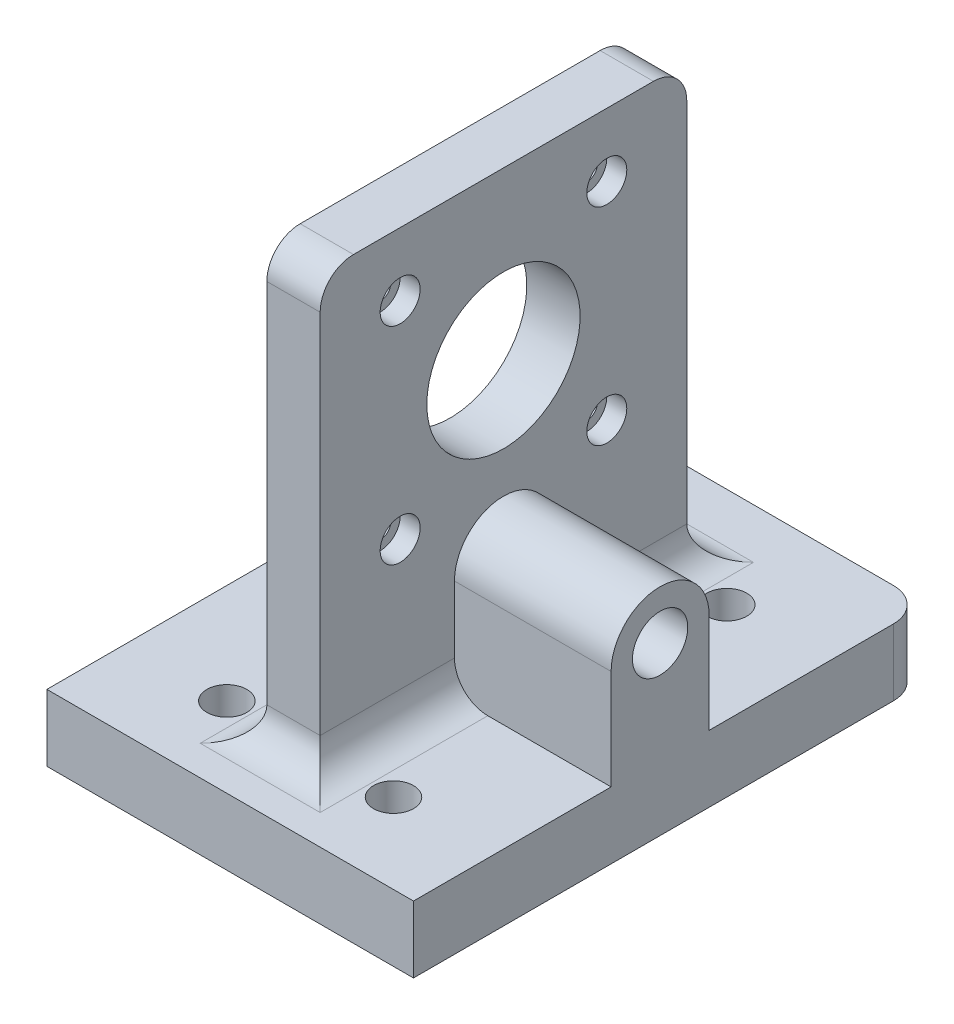
SolidWorks part; units mm, degrees
ref_plane "Front Plane" through (0, 0, 0) normal (0, 0, 1) x (1, 0, 0)
ref_plane "Top Plane" through (0, 0, 0) normal (0, 1, 0) x (1, 0, 0)
ref_plane "Right Plane" through (0, 0, 0) normal (1, 0, 0) x (0, 0, -1)
sketch "Sketch1" plane through (0, 0, 0) normal (0, 1, 0) x (1, 0, 0)
  line L1 (-27.5, 40) -> (27.5, 40)
  line L2 (-27.5, 40) -> (-27.5, -40)
  line L3 (-27.5, -40) -> (27.5, -40)
  line L4 (27.5, 40) -> (27.5, -40)
  line L5 (-27.5, 40) -> (27.5, -40) construction
  line L6 (-27.5, -40) -> (27.5, 40) construction
  point P0 (0, 0)
  dimension "D1" = 55
  dimension "D2" = 80
extrude "Boss-Extrude1" add sketch "Sketch1" along normal blind 10
sketch "Sketch6" plane through (0, 10, 0) normal (0, 1, 0) x (1, 0, 0)
  line L0 (-27.5, -40) -> (27.5, -40) construction
  circle A0 centre (-12.5, -25) radius 1.65
  dimension "D3" = 3.3
  dimension "D1" = 12.5
  dimension "D2" = 15
extrude "Cut-Extrude2" cut sketch "Sketch6" against normal blind 55
pattern_linear "LPattern1" count 3 spacing 25 along (0, 0, -1) of "Cut-Extrude2"
mirror "Mirror3" about plane through (0, 0, 0) normal (1, 0, 0) of "LPattern1", "Cut-Extrude2"
sketch "Sketch8" plane through (0, 10, 0) normal (0, 1, 0) x (1, 0, 0)
  line L1 (-4, 27.5) -> (4, 27.5)
  line L2 (-4, 27.5) -> (-4, -27.5)
  line L3 (-4, -27.5) -> (4, -27.5)
  line L4 (4, 27.5) -> (4, -27.5)
  line L5 (-4, 27.5) -> (4, -27.5) construction
  line L6 (-4, -27.5) -> (4, 27.5) construction
  point P0 (0, 0)
  dimension "D1" = 55
  dimension "D2" = 8
extrude "Boss-Extrude3" add sketch "Sketch8" along normal blind 65
fillet "Fillet3" radius 5 8 edges at (-27.5, 5, -40) (27.5, 5, -40) (0, 75, -27.5) (0, 75, 27.5) (4, 10, 0) (-4, 10, 0) (0, 10, -27.5) (0, 10, 27.5)
sketch "Sketch9" plane through (-4, 0, 0) normal (-1, 0, 0) x (0, 0, 1)
  line L0 (-22.5, 75) -> (22.5, 75) construction
  line L1 (-15.5, 65.5) -> (15.5, 65.5) construction
  line L2 (-15.5, 65.5) -> (-15.5, 34.5) construction
  line L3 (-15.5, 34.5) -> (15.5, 34.5) construction
  line L4 (15.5, 65.5) -> (15.5, 34.5) construction
  line L5 (-15.5, 65.5) -> (15.5, 34.5) construction
  line L6 (-15.5, 34.5) -> (15.5, 65.5) construction
  circle A0 centre (-15.5, 65.5) radius 1.6
  circle A1 centre (15.5, 65.5) radius 1.6
  circle A2 centre (-15.5, 34.5) radius 1.6
  circle A3 centre (15.5, 34.5) radius 1.6
  circle A4 centre (0, 50) radius 11.5
  point P0 (0, 50)
  dimension "D5" = 3.2
  dimension "D6" = 3.2
  dimension "D7" = 3.2
  dimension "D8" = 3.2
  dimension "D9" = 23
  dimension "D1" = 25
  dimension "D2" = 31
  dimension "D3" = 31
  dimension "D4" = 0
extrude "Cut-Extrude3" cut sketch "Sketch9" against normal through all
sketch "Sketch10" plane through (4, 0, 0) normal (1, 0, 0) x (0, 0, -1)
  circle A0 centre (-15.5, 65.5) radius 3
  circle A1 centre (15.5, 65.5) radius 3
  circle A2 centre (15.5, 34.5) radius 3
  circle A3 centre (-15.5, 34.5) radius 3
  dimension "D1" = 6
  dimension "D2" = 6
  dimension "D3" = 6
  dimension "D4" = 6
extrude "Cut-Extrude4" cut sketch "Sketch10" against normal blind 3
sketch "Sketch11" plane through (0, 10, 0) normal (0, 1, 0) x (1, 0, 0)
  circle A0 centre (-12.5, -25) radius 3
  dimension "D1" = 6
extrude "Cut-Extrude5" cut sketch "Sketch11" against normal blind 5 and the other way through all
pattern_linear "LPattern2" count 3 spacing 25 along (0, 0, -1) of "Cut-Extrude5"
mirror "Mirror4" about plane through (0, 0, 0) normal (1, 0, 0) of "LPattern2", "Cut-Extrude5"
sketch "Sketch12" plane through (0, 10, 0) normal (0, 1, 0) x (1, 0, 0)
  line L0 (12.5, -25) -> (12.5, -37) construction
  line L1 (12.5, -37) -> (-38.0557, -37)
  line L2 (-38.0557, -37) -> (-38.0557, -44.2873)
  line L3 (-38.0557, -44.2873) -> (40.3693, -44.2873)
  line L4 (40.3693, -44.2873) -> (40.3693, -37)
  line L5 (40.3693, -37) -> (12.5, -37)
  dimension "D1" = 12
extrude "Cut-Extrude6" cut sketch "Sketch12" against normal blind 10
sketch "Sketch13" plane through (4, 0, 0) normal (1, 0, 0) x (0, 0, -1)
  line L0 (-7.35, 25) -> (-7.35, 10)
  line L1 (32.5, 10) -> (-32.5, 10) construction
  line L2 (7.35, 25) -> (7.35, 10)
  line L3 (-7.35, 10) -> (-7.35, 0)
  line L4 (-37, 0) -> (35, 0) construction
  line L5 (-7.35, 0) -> (7.35, 0)
  line L6 (7.35, 0) -> (7.35, 10)
  circle A1 centre (0, 25) radius 4.15
  arc A2 (7.35, 25) -> (-7.35, 25) centre (0, 25) ccw
  circle A4 centre (0, 25) radius 7.35 construction
  point P2 (7.35, 25)
  dimension "D1" = 8.3
  dimension "D2" = 25
  dimension "D3" = 3.2
extrude "Boss-Extrude4" add sketch "Sketch13" along normal up to surface (23.5 mm away) up to face at (27.5, 5, 1)
